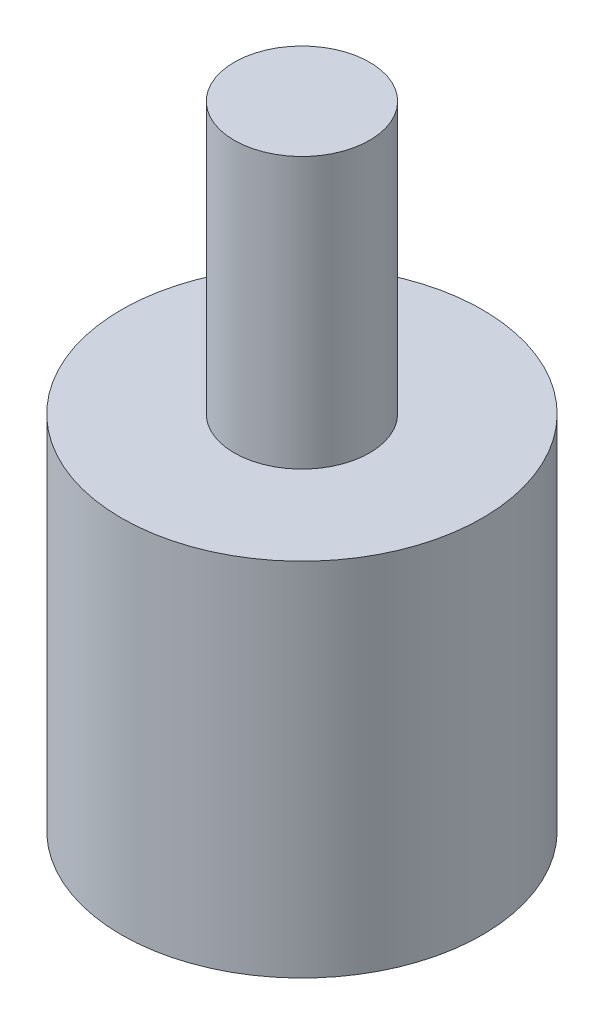
SolidWorks part; units mm, degrees
ref_plane "Front Plane" through (0, 0, 0) normal (0, 0, 1) x (1, 0, 0)
ref_plane "Top Plane" through (0, 0, 0) normal (0, 1, 0) x (1, 0, 0)
ref_plane "Right Plane" through (0, 0, 0) normal (1, 0, 0) x (0, 0, -1)
sketch "Sketch1" plane through (0, 0, 0) normal (0, 1, 0) x (1, 0, 0)
  circle A0 centre (0, 0) radius 4
  dimension "D1" = 8
extrude "Boss-Extrude1" add sketch "Sketch1" along normal blind 8
sketch "Sketch2" plane through (0, 8, 0) normal (0, 1, 0) x (1, 0, 0)
  circle A0 centre (0, 0) radius 1.5
  dimension "D1" = 3
extrude "Boss-Extrude2" add sketch "Sketch2" along normal blind 6
